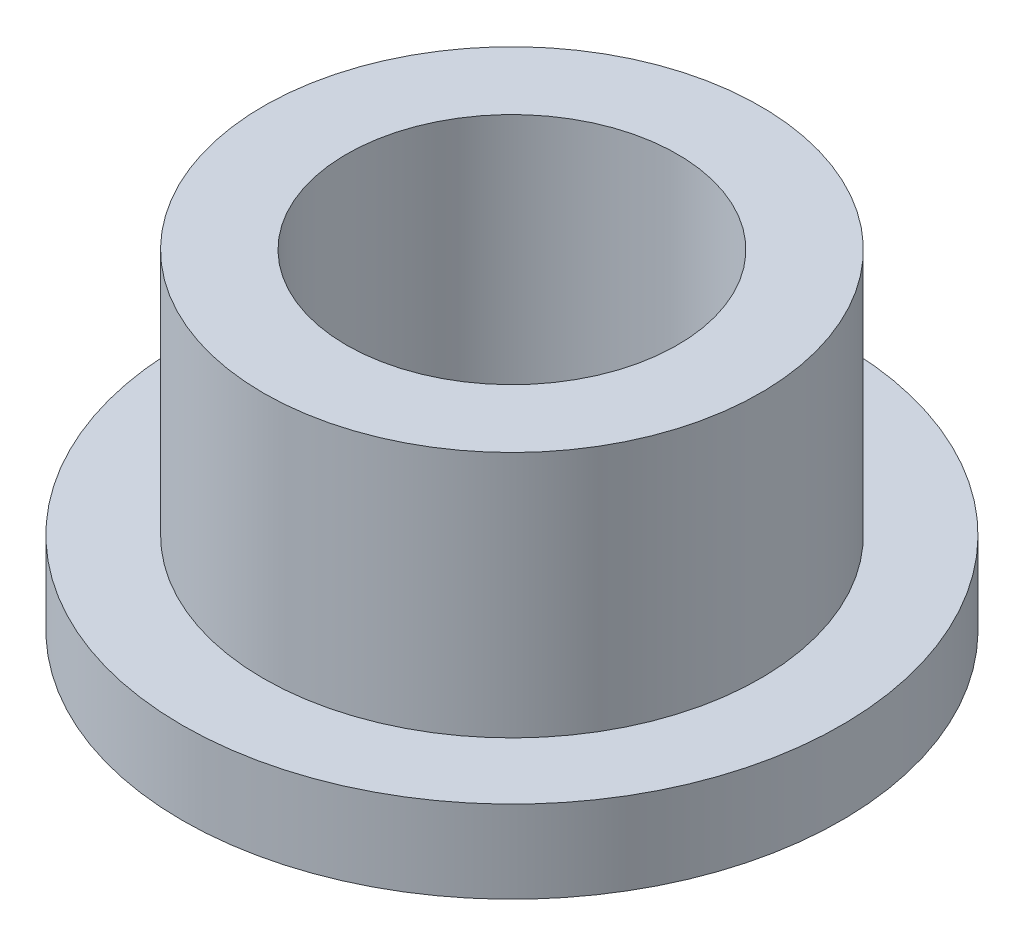
SolidWorks part; units mm, degrees
ref_plane "Front" through (0, 0, 0) normal (0, 0, 1) x (1, 0, 0)
ref_plane "Top" through (0, 0, 0) normal (0, 1, 0) x (1, 0, 0)
ref_plane "Right" through (0, 0, 0) normal (1, 0, 0) x (0, 0, -1)
sketch "Sketch1" plane through (0, 0, 0) normal (0, 1, 0) x (1, 0, 0)
  circle A0 centre (0, 0) radius 3.1877
  circle A1 centre (0, 0) radius 4.7879
  circle A2 centre (0, 0) radius 6.35
  dimension "ID" = 6.3754
  dimension "OD" = 9.5758
  dimension "FlangeOD" = 12.7
sketch "Sketch2" plane through (0, 0, 0) normal (0, 1, 0) x (1, 0, 0)
  circle A0 centre (0, 0) radius 3.1877 construction
  circle A1 centre (0, 0) radius 4.7879 construction
  circle A2 centre (0, 0) radius 3.1877
  circle A3 centre (0, 0) radius 4.7879
extrude "Boss-Extrude1" add sketch "Sketch2" along normal blind 6.35
sketch "Sketch3" plane through (0, 0, 0) normal (0, 1, 0) x (1, 0, 0)
  circle A0 centre (0, 0) radius 6.35 construction
  circle A1 centre (0, 0) radius 4.7879 construction
  circle A2 centre (0, 0) radius 6.35
  circle A3 centre (0, 0) radius 4.7879
extrude "Boss-Extrude2" add sketch "Sketch3" along normal blind 1.5875
